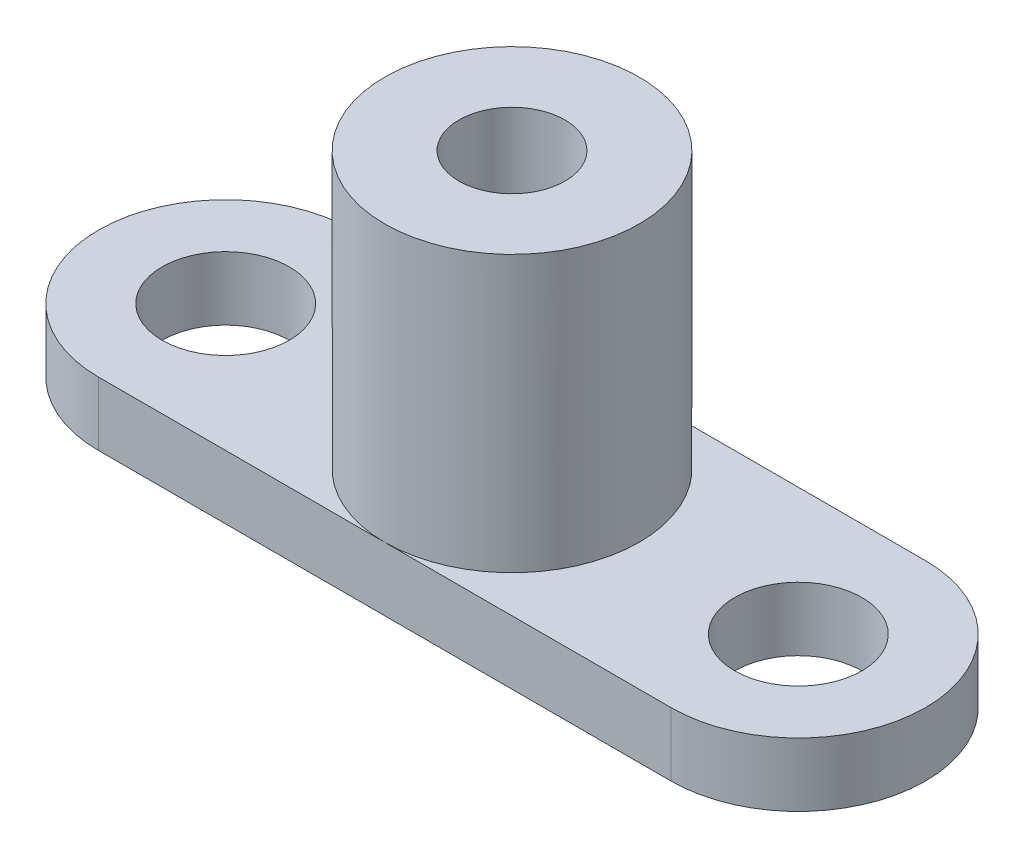
SolidWorks part; units mm, degrees
ref_plane "前视基准面" through (0, 0, 0) normal (0, 0, 1) x (1, 0, 0)
ref_plane "上视基准面" through (0, 0, 0) normal (0, 1, 0) x (1, 0, 0)
ref_plane "右视基准面" through (0, 0, 0) normal (1, 0, 0) x (0, 0, -1)
sketch "草图1" plane through (0, 0, 0) normal (0, 1, 0) x (1, 0, 0)
  line L0 (-13.5, 6) -> (13.5, 6)
  line L1 (-13.5, -6) -> (13.5, -6)
  line L4 (-13.5, 6) -> (-13.5, -6)
  line L8 (13.5, 6) -> (13.5, -6)
  circle A0 centre (-13.5, 0) radius 6
  circle A1 centre (13.5, 0) radius 6
  dimension "D1" = 12
  dimension "D2" = 13.5
  dimension "D3" = 13.5
extrude "凸台-拉伸1" add sketch "草图1" along normal blind 3
sketch "草图2" plane through (0, 3, 0) normal (0, 1, 0) x (1, 0, 0)
  circle A0 centre (0, 0) radius 6
extrude "凸台-拉伸2" add sketch "草图2" along normal blind 13
hole_wizard "M6 螺纹孔1" positions "草图3" profile "草图5" tap size "M6" standard "GB"
sketch "草图3" plane through (0, 16, 0) normal (0, 1, 0) x (1, 0, 0)
  point P0 (0, 0)
cosmetic thread "孔螺蚊线1" parameters "D1"=12, "D2"=6
sketch "草图5" plane through (0, 16, 0) normal (1, 0, 0) x (0, 0, 1)
  line L0 (0, 0) -> (0, 13.5022)
  line L1 (0, 13.5022) -> (2.5, 12)
  line L2 (2.5, 12) -> (2.5, 0)
  line L5 (2.5, 0) -> (0, 0)
  line L10 (0, 13.5022) -> (-2.5, 12) construction
  line L11 (0, -6.35) -> (0, 107.95) construction
  dimension "螺纹孔钻头直径" = 5
  dimension "螺纹孔钻头深度" = 12
  dimension "导头角度" = 118
sketch "草图6" plane through (0, 3, 0) normal (0, 1, 0) x (1, 0, 0)
  circle A0 centre (-13.5, 0) radius 3
  circle A1 centre (13.5, 0) radius 3
  dimension "D1" = 6
  dimension "D2" = 6
extrude "切除-拉伸1" cut sketch "草图6" against normal blind 10
